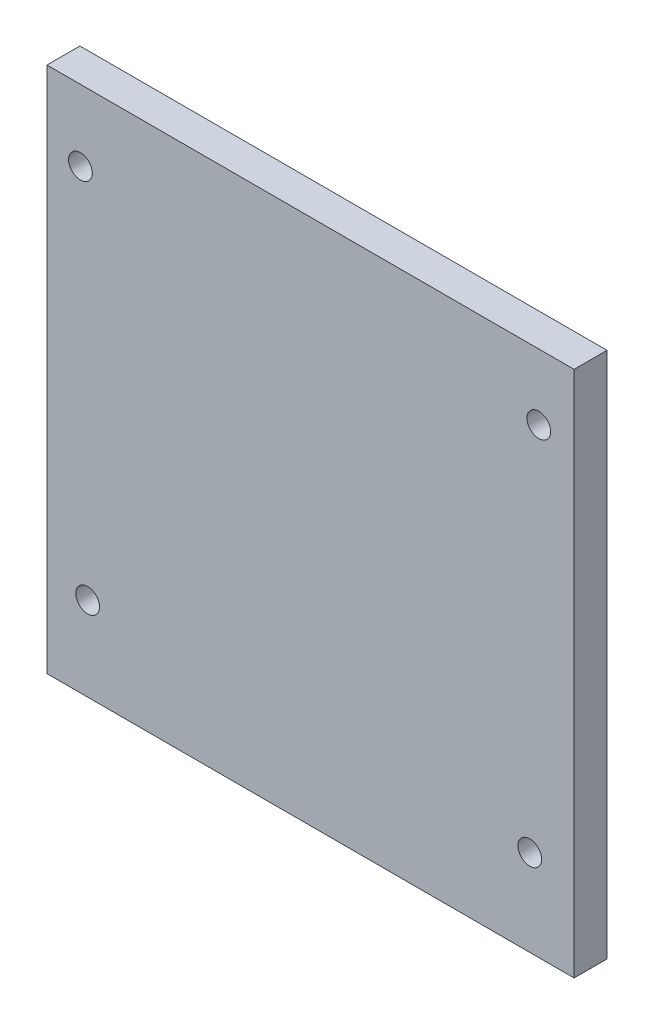
SolidWorks part; units mm, degrees
ref_plane "Front Plane" through (0, 0, 0) normal (0, 0, 1) x (1, 0, 0)
ref_plane "Top Plane" through (0, 0, 0) normal (0, 1, 0) x (1, 0, 0)
ref_plane "Right Plane" through (0, 0, 0) normal (1, 0, 0) x (0, 0, -1)
sketch "Sketch1" plane through (0, 0, 0) normal (0, 0, 1) x (1, 0, 0)
  line L1 (-50.8, -50.8) -> (50.8, -50.8)
  line L2 (-50.8, -50.8) -> (-50.8, 50.8)
  line L3 (-50.8, 50.8) -> (50.8, 50.8)
  line L4 (50.8, -50.8) -> (50.8, 50.8)
  line L5 (-50.8, -50.8) -> (50.8, 50.8) construction
  line L6 (-50.8, 50.8) -> (50.8, -50.8) construction
  point P0 (0, 0)
  dimension "D1" = 101.6
  dimension "D2" = 101.6
extrude "Boss-Extrude1" add sketch "Sketch1" along normal blind 6.35
sketch "Sketch2" plane through (0, 0, 0) normal (0, 0, -1) x (-1, 0, 0)
  circle A0 centre (-42.2593, -34.1231) radius 2.286 construction
  circle A1 centre (-42.2593, -34.1231) radius 2.286
  circle A2 centre (42.9594, -34.611) radius 2.286 construction
  circle A3 centre (42.9594, -34.611) radius 2.286
  circle A4 centre (44.3532, 37.1057) radius 2.286 construction
  circle A5 centre (-44.009, 38.1285) radius 2.286 construction
  circle A6 centre (44.3532, 37.1057) radius 2.286
  circle A7 centre (-44.009, 38.1285) radius 2.286
extrude "Cut-Extrude1" cut sketch "Sketch2" against normal through all
equation "\"D1@Boss-Extrude1\" = \"material\""
equation "\"material\"=\"GMaterial@Platform.assembly\""
